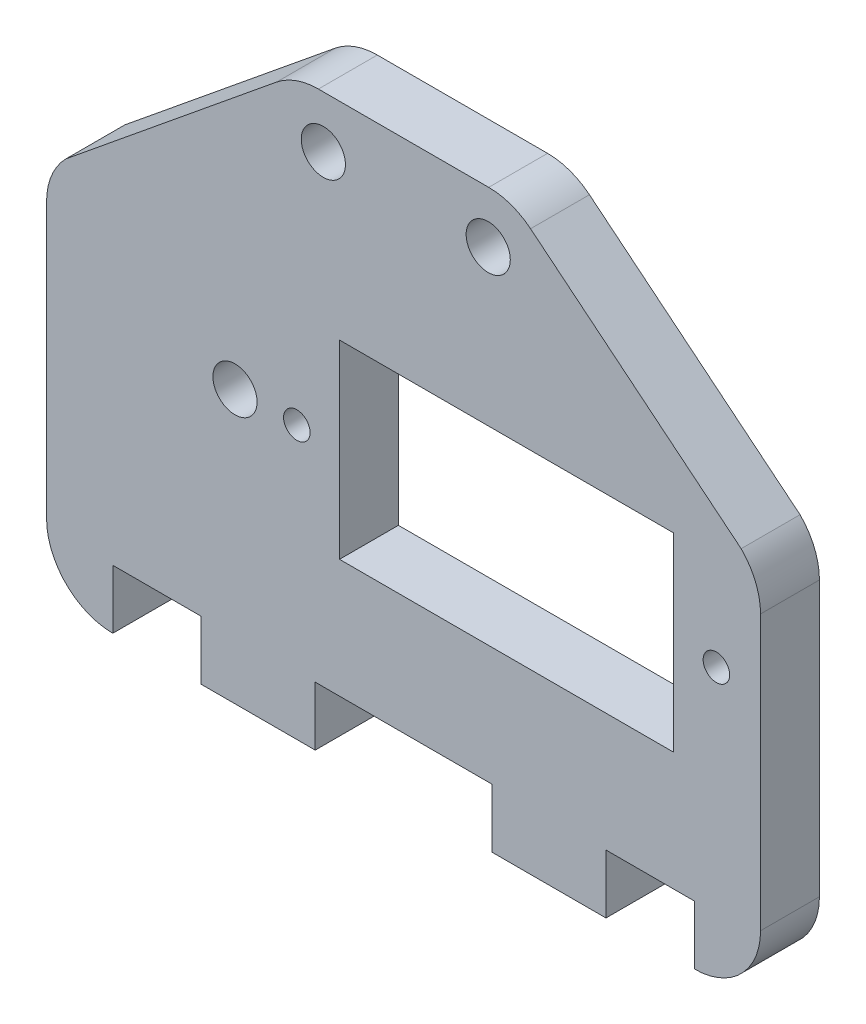
SolidWorks part; units mm, degrees
material "Beech"
ref_plane "Front Plane" through (0, 0, 0) normal (0, 0, 1) x (1, 0, 0)
ref_plane "Top Plane" through (0, 0, 0) normal (0, 1, 0) x (1, 0, 0)
ref_plane "Right Plane" through (0, 0, 0) normal (1, 0, 0) x (0, 0, -1)
sketch "Sketch1" plane through (0, 0, 0) normal (0, 0, 1) x (1, 0, 0)
  line L0 (48.5, 4.6604) -> (48.5, 23.2965)
  line L1 (30.0334, 39.1604) -> (18.4666, 39.1604)
  line L2 (0, 23.2965) -> (0, 4.6604)
  line L3 (42.6, 25.1104) -> (19.9, 25.1104)
  line L4 (19.9, 12.2104) -> (42.6, 12.2104)
  line L5 (42.6, 25.1104) -> (42.6, 12.2104)
  line L6 (19.9, 25.1104) -> (19.9, 12.2104)
  line L7 (47.182, 26.4784) -> (32.8779, 38.1473)
  line L8 (15.6221, 38.1473) -> (1.318, 26.4784)
  line L9 (4.5, 0.1604) -> (4.5, 4.1604)
  line L10 (4.5, 4.1604) -> (10.5, 4.1604)
  line L11 (10.5, 4.1604) -> (10.5, 0.1604)
  line L12 (44, 0.1604) -> (44, 4.1604)
  line L13 (44, 4.1604) -> (38, 4.1604)
  line L14 (38, 4.1604) -> (38, 0.1604)
  line L15 (18.25, 4.1604) -> (30.25, 4.1604)
  line L16 (30.25, 4.1604) -> (30.25, 0.1604)
  line L17 (18.25, 4.1604) -> (18.25, 0.1604)
  line L18 (10.5, 0.1604) -> (18.25, 0.1604)
  line L19 (30.25, 0.1604) -> (38, 0.1604)
  circle A0 centre (12.8, 18.6604) radius 1.5
  circle A1 centre (18.8, 35.6304) radius 1.5
  circle A2 centre (30, 35.6304) radius 1.5
  arc A3 (48.5, 23.2965) -> (47.182, 26.4784) centre (44, 23.2965) ccw
  arc A4 (1.318, 26.4784) -> (0, 23.2965) centre (4.5, 23.2965) ccw
  arc A5 (44, 0.1604) -> (48.5, 4.6604) centre (44, 4.6604) ccw
  arc A6 (0, 4.6604) -> (4.5, 0.1604) centre (4.5, 4.6604) ccw
  arc A7 (32.8779, 38.1473) -> (30.0334, 39.1604) centre (30.0334, 34.6604) ccw
  arc A8 (18.4666, 39.1604) -> (15.6221, 38.1473) centre (18.4666, 34.6604) ccw
  circle A9 centre (17, 18.6604) radius 0.9
  circle A10 centre (45.5, 18.6604) radius 0.9
extrude "Boss-Extrude1" add sketch "Sketch1" along normal blind 4
